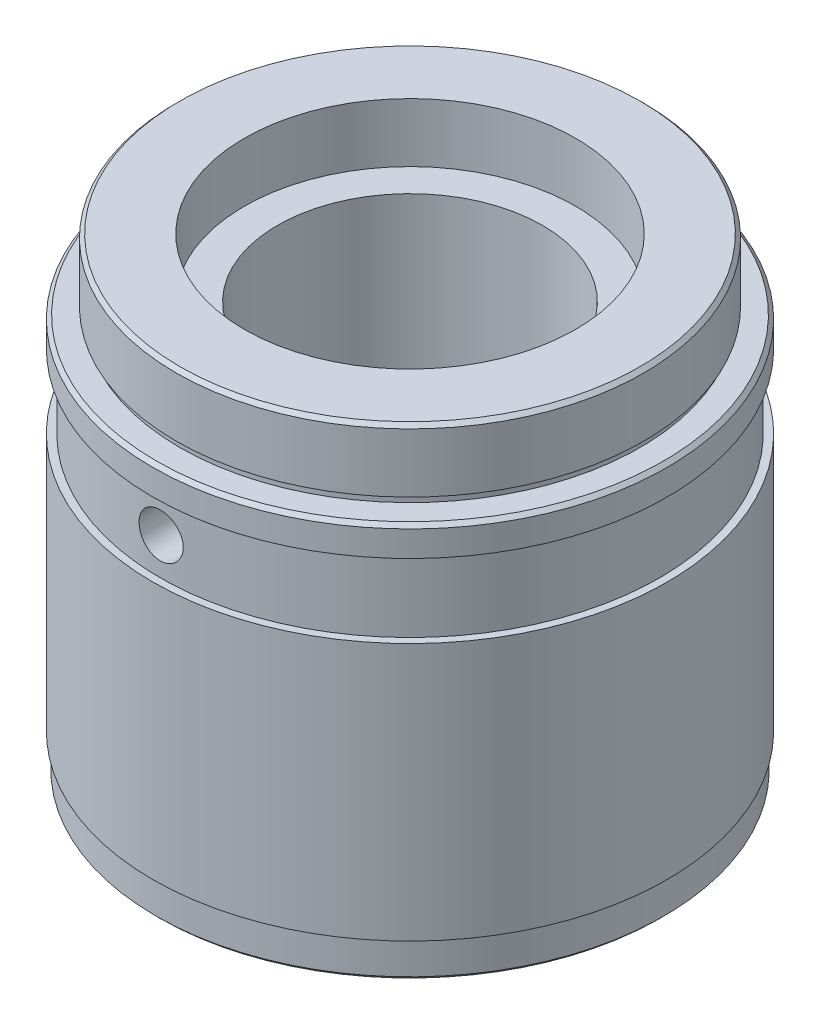
SolidWorks part; units mm, degrees
ref_plane "Front Plane" through (0, 0, 0) normal (0, 0, 1) x (1, 0, 0)
ref_plane "Top Plane" through (0, 0, 0) normal (0, 1, 0) x (1, 0, 0)
ref_plane "Right Plane" through (0, 0, 0) normal (1, 0, 0) x (0, 0, -1)
sketch "Sketch1" plane through (0, 0, 0) normal (0, 1, 0) x (1, 0, 0)
  circle A0 centre (0, 0) radius 34.925
extrude "Main Body" add sketch "Sketch1" along normal blind 63.5 separate body
sketch "Sketch2" plane through (0, 0, 0) normal (0, -1, 0) x (1, 0, 0)
  circle A0 centre (0, 0) radius 34.5
extrude "Bottom Step" cut sketch "Sketch2" against normal blind 5 flip side to cut
sketch "Sketch3" plane through (0, 63.5, 0) normal (0, 1, 0) x (1, 0, 0)
  circle A0 centre (0, 0) radius 31.75
extrude "Top Diameter" cut sketch "Sketch3" against normal blind 9.52 flip side to cut
sketch "Sketch4" plane through (0, 53.98, 0) normal (0, 1, 0) x (1, 0, 0)
  circle A0 centre (0, 0) radius 31.25
extrude "Cut-Extrude3" cut sketch "Sketch4" along normal blind 1 flip side to cut
sketch "Sketch5" plane through (0, 63.5, 0) normal (0, 1, 0) x (1, 0, 0)
  circle A0 centre (0, 0) radius 22.5
extrude "Insert Bore" cut sketch "Sketch5" against normal blind 8
sketch "Sketch6" plane through (0, 0, 0) normal (0, -1, 0) x (1, 0, 0)
  circle A0 centre (0, 0) radius 18
extrude "Cut-Extrude5" cut sketch "Sketch6" against normal through all
sketch "Sketch7" plane through (0, 0, 0) normal (0, -1, 0) x (1, 0, 0)
  circle A0 centre (0, 0) radius 21
extrude "Cut-Extrude6" cut sketch "Sketch7" against normal blind 5
chamfer "Bottom Edge Chamfer" distance 0.5 angle 45 1 edges at (0, 0, -34.5)
chamfer "Top Face Chamfer" distance 0.5 angle 45 1 edges at (0, 63.5, 31.75)
chamfer "Body To Top Face Chamfer" distance 0.5 angle 45 1 edges at (0, 53.98, 34.925)
sketch "Sketch8" plane through (0, 0, 0) normal (0, 0, 1) x (1, 0, 0)
  line L0 (34.925, 5) -> (34.925, 53.48) construction
  line L1 (33.925, 40) -> (34.925, 40)
  line L2 (33.925, 40) -> (33.925, 50)
  line L3 (33.925, 50) -> (34.925, 50)
  line L4 (34.925, 40) -> (34.925, 50)
  line L5 (33.925, 40) -> (34.925, 50) construction
  line L6 (33.925, 50) -> (34.925, 40) construction
  line L7 (0, 0) -> (0, 63.5) construction
  point P4 (34.425, 45)
revolve "Oil Groove" cut sketch "Sketch8" angle 360 about L7
sketch "Sketch9" plane through (0, 0, 0) normal (0, 0, 1) x (1, 0, 0)
  circle A0 centre (0, 45) radius 3
extrude "Oil Hole" cut sketch "Sketch9" along normal through all
